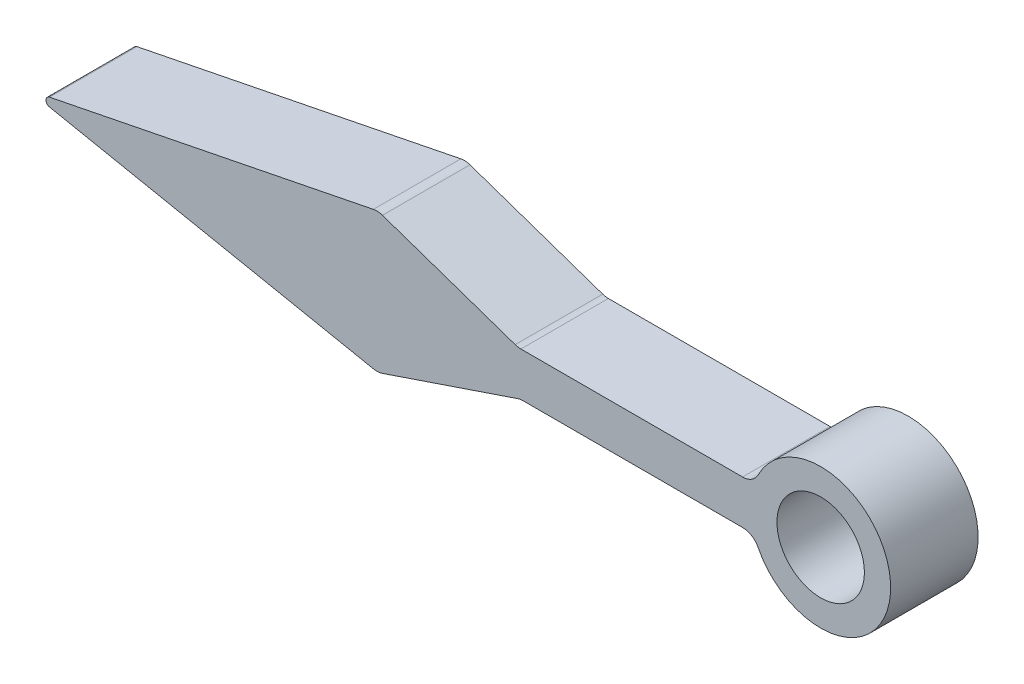
SolidWorks part; units mm, degrees
ref_plane "Plan de face" through (0, 0, 0) normal (0, 0, 1) x (1, 0, 0)
ref_plane "Plan de dessus" through (0, 0, 0) normal (0, 1, 0) x (1, 0, 0)
ref_plane "Plan de droite" through (0, 0, 0) normal (1, 0, 0) x (0, 0, -1)
sketch "Esquisse1" plane through (0, 0, 0) normal (0, 0, 1) x (1, 0, 0)
  line L0 (0, -23.1811) -> (0, 26.8189) construction
  line L1 (-45.2997, 0) -> (4.7003, 0) construction
  line L3 (-3.7997, 1.25) -> (-17.2997, 1.25)
  line L5 (-17.1705, -1.25) -> (-3.7997, -1.25)
  line L6 (-17.2997, 1.25) -> (-25.2997, 4)
  line L7 (-25.2997, 4) -> (-45.2997, 0)
  line L8 (-45.2997, 0) -> (-25.2997, -4)
  line L9 (-25.2997, -4) -> (-17.1705, -1.25)
  line L10 (-25.2997, 4) -> (-25.2997, -4) construction
  arc A0 (-3.7997, 1.25) -> (-3.7997, -1.25) centre (0, 0) cw
  circle A1 centre (0, 0) radius 2.5
  point P7 (0, 0)
  dimension "D3" = 4
  dimension "D4" = 1.5
  dimension "D1" = 50
  dimension "D5" = 2.5
  dimension "D6" = 13.5
  dimension "D7" = 8
  dimension "D8" = 20
  dimension "D9" = 8
  dimension "D11" = 150
extrude "Boss.-Extru.1" add sketch "Esquisse1" along normal blind 5
fillet "Congé1" radius 1 6 edges at (-25.2997, 4, 2.5) (-17.2997, 1.25, 2.5) (-3.7997, 1.25, 2.5) (-3.7997, -1.25, 2.5) (-17.1705, -1.25, 2.5) (-25.2997, -4, 2.5)
fillet "Congé2" radius 0.25 1 edges at (-45.2997, 0, 2.5)
